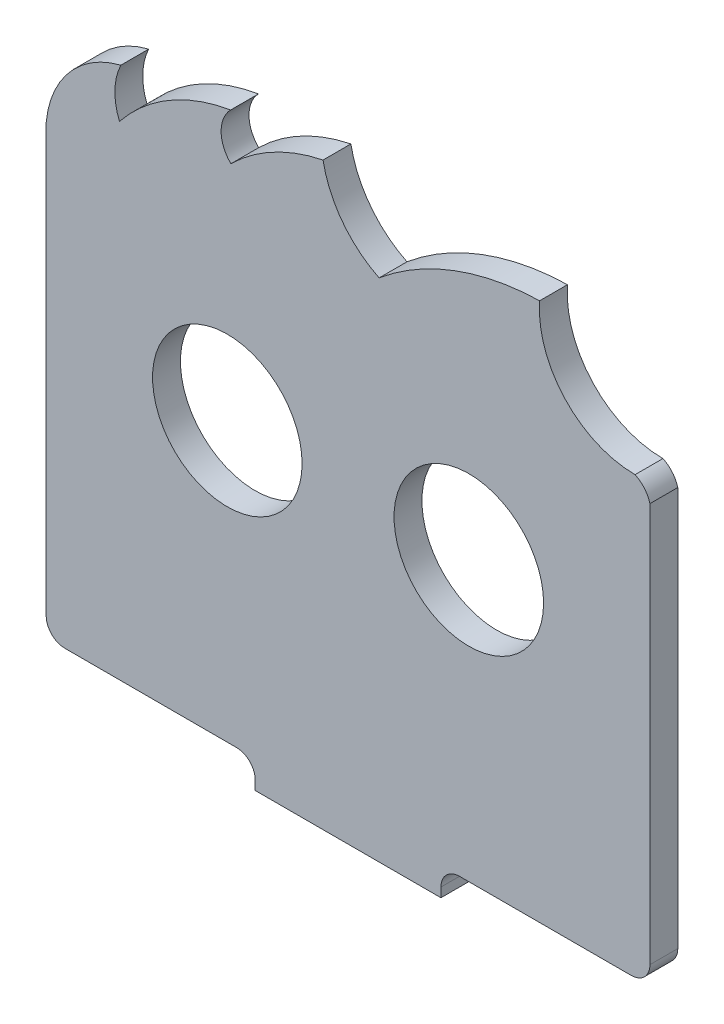
SolidWorks part; units mm, degrees
ref_plane "Alzado" through (0, 0, 0) normal (0, 0, 1) x (1, 0, 0)
ref_plane "Planta" through (0, 0, 0) normal (0, 1, 0) x (1, 0, 0)
ref_plane "Vista lateral" through (0, 0, 0) normal (1, 0, 0) x (0, 0, -1)
sketch "Croquis1" plane through (0, 0, 0) normal (0, 0, 1) x (1, 0, 0)
  line L0 (-30.9388, -8.0456) -> (-10.9388, -8.0456)
  line L1 (-33.9388, 24.9544) -> (-7.9388, 24.9544) construction
  line L2 (-20.9388, 24.9544) -> (-20.9388, -8.0456) construction
  line L3 (-30.9388, -8.0456) -> (-30.9388, -7.0442)
  line L5 (-32.9374, -5.0442) -> (-51.4302, -5.0309)
  line L6 (-53.4388, 43.0128) -> (-53.4388, -2.9883)
  line L7 (11.5612, -3.0343) -> (11.5612, 39.9544)
  line L8 (9.5498, -5.0456) -> (-8.9388, -5.0456)
  line L10 (-10.9388, -8.0456) -> (-10.9388, -7.0456)
  circle A0 centre (-7.9388, 24.9544) radius 8.05
  circle A1 centre (-33.9388, 24.9544) radius 8.05
  arc A2 (-30.9388, -7.0442) -> (-32.9374, -5.0442) centre (-32.9388, -7.0442) ccw
  arc A3 (-53.4388, -2.9883) -> (-51.4302, -5.0309) centre (-51.4277, -3.0195) ccw
  arc A4 (-45.4026, 52.3515) -> (-53.4388, 43.0128) centre (-42.8405, 42.0198) ccw
  arc A5 (-45.4026, 52.3515) -> (-45.5497, 47.0288) centre (-39.5276, 49.5259) ccw
  arc A6 (-33.5821, 54.0841) -> (-45.5497, 47.0288) centre (-30.394, 34.9986) ccw
  arc A7 (-33.5821, 54.0841) -> (-33.559, 49.0841) centre (-31.0706, 51.5956) ccw
  arc A8 (-23.6335, 54.394) -> (-33.559, 49.0841) centre (-19.6409, 34.9994) ccw
  arc A9 (-23.6335, 54.394) -> (-17.5966, 46.4218) centre (-12.6428, 56.4447) ccw
  arc A10 (-0.3161, 52.9296) -> (-17.5966, 46.4218) centre (0.3341, 25.0062) ccw
  arc A11 (-0.3161, 52.9296) -> (9.9633, 41.8569) centre (9.9633, 52.1647) ccw
  arc A12 (11.5612, 39.9544) -> (9.9633, 41.8569) centre (8.6712, 39.1495) ccw
  arc A13 (9.5498, -5.0456) -> (11.5612, -3.0343) centre (9.5498, -3.0343) ccw
  arc A14 (-10.9388, -7.0456) -> (-8.9388, -5.0456) centre (-8.9388, -7.0456) cw
  dimension "D1" = 2
extrude "Saliente-Extruir1" add sketch "Croquis1" along normal blind 3
sketch "Croquis2" plane through (0, 0, 3) normal (0, 0, 1) x (1, 0, 0)
  line L0 (-30.9388, -8.0456) -> (-30.9388, -5.0456)
  line L1 (-30.9388, -5.0456) -> (-10.9388, -5.0456)
  line L2 (-10.9388, -5.0456) -> (-10.9388, -8.0456)
  line L3 (-10.9388, -8.0456) -> (-30.9388, -8.0456)
extrude "Saliente-Extruir2" add sketch "Croquis2" against normal blind 11
sketch "Croquis3" plane through (0, -5.0456, 0) normal (0, 1, 0) x (1, 0, 0)
  line L0 (-20.9388, 0) -> (-20.9388, 8) construction
  line L2 (-30.9388, 8) -> (-10.9388, 8) construction
  line L3 (-10.9388, 0) -> (-30.9388, 0) construction
  line L6 (-10.9388, 0) -> (-30.9388, 0) construction
  circle A0 centre (-14.9388, 3.5) radius 1.5
  circle A1 centre (-26.9388, 3.5) radius 1.5
  dimension "D1" = 6
  dimension "D2" = 3.5
extrude "Cortar-Extruir1" cut sketch "Croquis3" against normal blind 3
fillet "Redondeo2" radius 2 2 edges at (-30.9388, -6.5456, -8) (-10.9388, -6.5456, -8)
sketch "Croquis4" plane through (0, -5.0456, 0) normal (0, 1, 0) x (1, 0, 0)
  circle A0 centre (-26.9388, 3.5) radius 2.25
  circle A1 centre (-14.9388, 3.5) radius 2.25
extrude "Cortar-Extruir2" cut sketch "Croquis4" against normal blind 1
